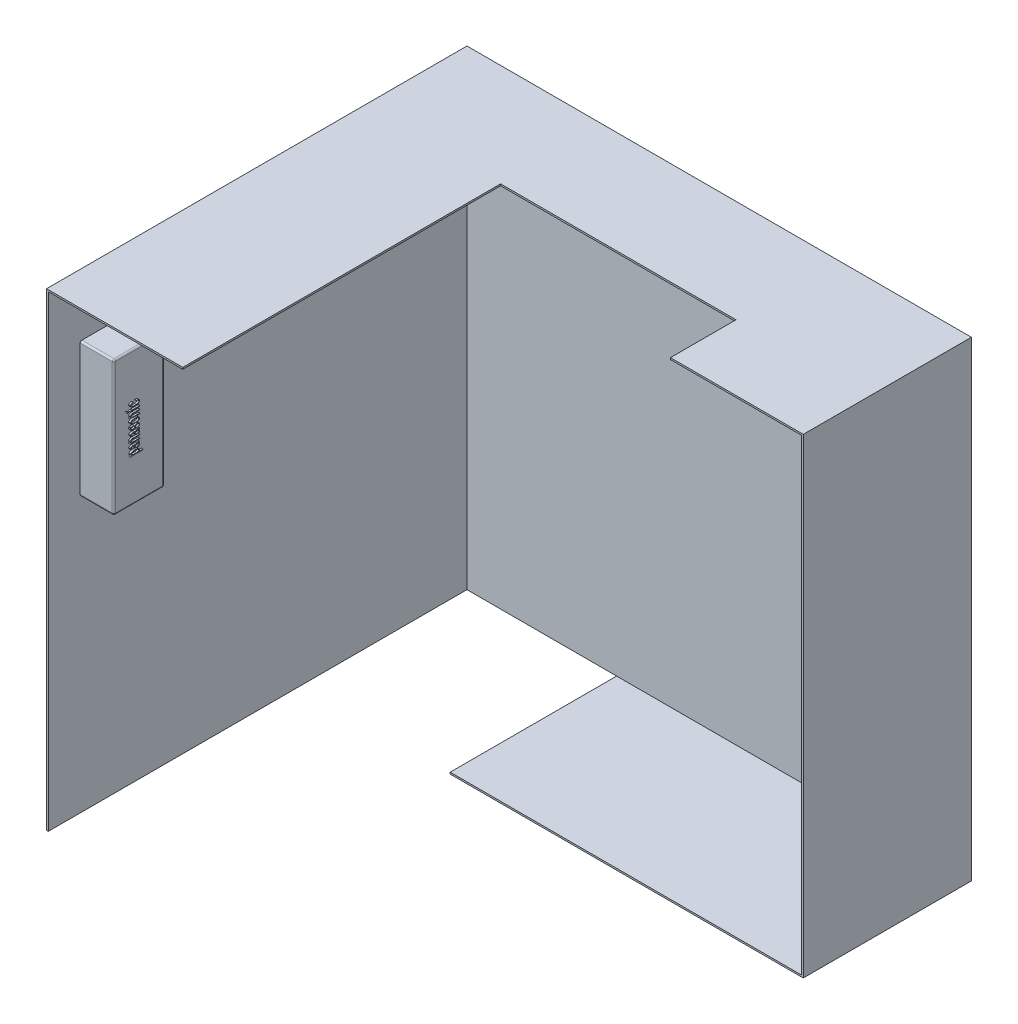
SolidWorks part; units mm, degrees
ref_plane "前视基准面" through (0, 0, 0) normal (0, 0, 1) x (1, 0, 0)
ref_plane "上视基准面" through (0, 0, 0) normal (0, 1, 0) x (1, 0, 0)
ref_plane "右视基准面" through (0, 0, 0) normal (1, 0, 0) x (0, 0, -1)
sketch "草图1" plane through (0, 0, 0) normal (0, 0, 1) x (1, 0, 0)
  line L1 (-1500, -1400) -> (1500, -1400)
  line L2 (-1500, -1400) -> (-1500, 1400)
  line L3 (-1500, 1400) -> (1500, 1400)
  line L4 (1500, -1400) -> (1500, 1400)
  line L5 (-1500, -1400) -> (1500, 1400) construction
  line L6 (-1500, 1400) -> (1500, -1400) construction
  point P0 (0, 0)
  dimension "D1" = 3000
  dimension "D2" = 2800
extrude "凸台-拉伸1" add sketch "草图1" along normal blind 1000
shell "抽壳1" thickness 10
sketch "草图2" plane through (0, -1400, 0) normal (0, -1, 0) x (1, 0, 0)
  line L1 (-1500, 0) -> (-600, 0)
  line L2 (-1500, 0) -> (-1500, 2000)
  line L3 (-1500, 2000) -> (-600, 2000)
  line L4 (-600, 0) -> (-600, 2000)
  dimension "D1" = 900
  dimension "D2" = 2000
extrude "切除-拉伸1" cut sketch "草图2" against normal up to surface (10 mm away) up to face at (0, -1390, 505)
sketch "草图3" plane through (0, 1390, 0) normal (0, -1, 0) x (1, 0, 0)
  line L1 (-1490, 1000) -> (-1490, 10) construction
  line L2 (-690, 610) -> (710, 610)
  line L3 (-690, 610) -> (-690, 1216.1433)
  line L4 (-690, 1216.1433) -> (710, 1216.1433)
  line L5 (710, 610) -> (710, 1216.1433)
  line L6 (-690, 610) -> (710, 1216.1433) construction
  line L7 (-690, 1216.1433) -> (710, 610) construction
  line L8 (1490, 10) -> (-1490, 10) construction
  point P2 (10, 913.0717)
  dimension "D1" = 800
  dimension "D2" = 600
  dimension "D3" = 1400
extrude "切除-拉伸2" cut sketch "草图3" against normal up to surface (10 mm away) up to face at (0, 1400, 500)
ref_plane "基准面1" through (-1490, -1390, 1000) normal (0, -1, 0) x (-1, 0, 0)
sketch "草图6" plane through (0, 0, 1000) normal (0, 0, 1) x (1, 0, 0)
  line L6 (-1490, 1390) -> (-690, 1390)
  line L7 (-690, 1390) -> (-690, 1400)
  line L8 (-690, 1400) -> (-1500, 1400)
  line L9 (-1500, 1400) -> (-1500, -1390)
  line L10 (-1500, -1390) -> (-1490, -1390)
  line L11 (-1490, -1390) -> (-1490, 1390)
  line L12 (-1490, 1390) -> (-690, 1390)
  line L13 (-690, 1390) -> (-690, 1400)
  line L14 (-690, 1400) -> (-1500, 1400)
  line L15 (-1500, 1400) -> (-1500, -1390)
  line L16 (-1500, -1390) -> (-1490, -1390)
  line L17 (-1490, -1390) -> (-1490, 1390)
  dimension "D1" = 0
extrude "凸台-拉伸2" add sketch "草图6" along normal blind 1500
sketch "草图7" plane through (-1490, 0, 0) normal (1, 0, 0) x (0, 0, -1)
  line L0 (-2500, 1390) -> (-10, 1390) construction
  line L1 (-2310, 1040) -> (-2010, 1040)
  line L2 (-2310, 1040) -> (-2310, 240)
  line L3 (-2310, 240) -> (-2010, 240)
  line L4 (-2010, 1040) -> (-2010, 240)
  line L5 (-10, 1390) -> (-10, -1390) construction
  dimension "D1" = 300
  dimension "D2" = 800
  dimension "D3" = 350
  dimension "D4" = 2000
extrude "凸台-拉伸3" add sketch "草图7" along normal blind 200
fillet "圆角1" radius 10 8 edges at (-1390, 1040, 2010) (-1390, 240, 2010) (-1390, 240, 2310) (-1390, 1040, 2310) (-1290, 1040, 2160) (-1290, 240, 2160) (-1290, 640, 2010) (-1290, 640, 2310)
sketch "草图9" plane through (-1290, 0, 0) normal (1, 0, 0) x (0, 0, -1)
  line L0 (-2160, 1030) -> (-2160, 250) construction
  line L1 (-2020, 1030) -> (-2300, 1030) construction
  line L2 (-2300, 250) -> (-2020, 250) construction
  text T0 "panasonic" font "汉仪长仿宋体" height 80
extrude "凸台-拉伸5" add sketch "草图9" along normal blind 10
